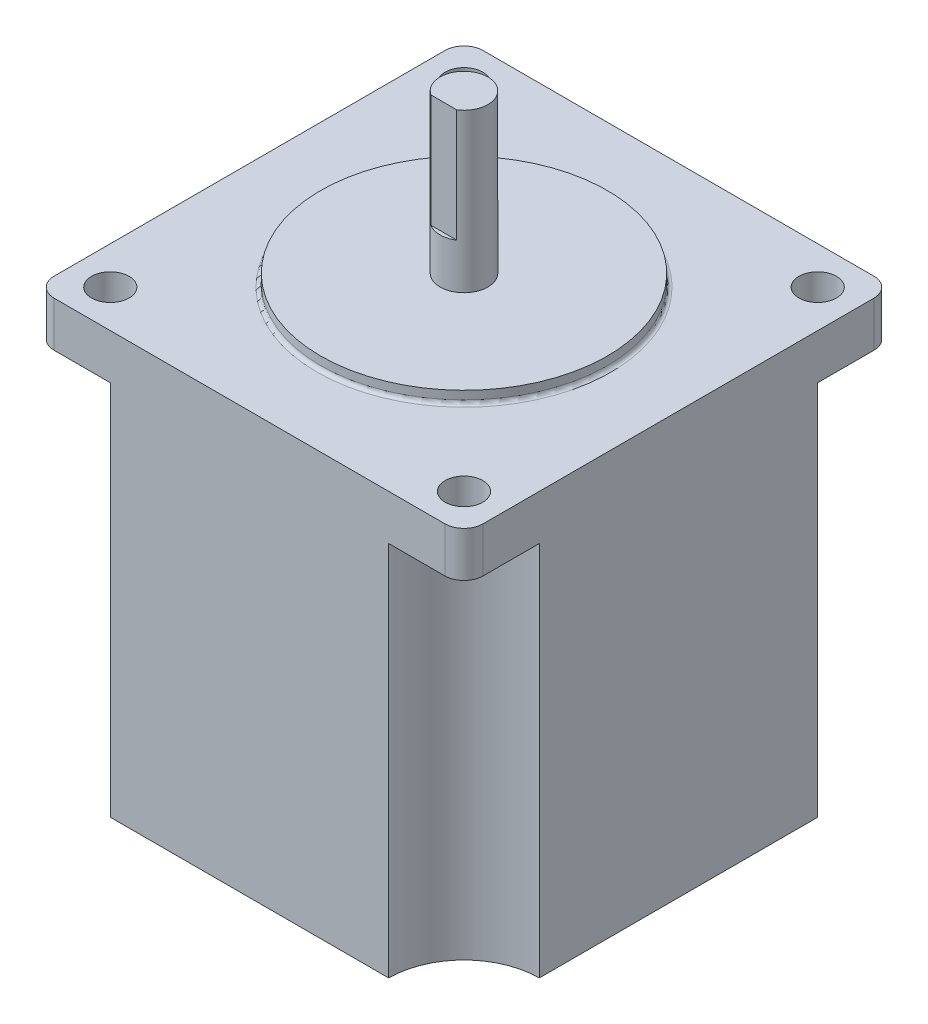
SolidWorks part; units mm, degrees
ref_plane "Front Plane" through (0, 0, 0) normal (0, 0, 1) x (1, 0, 0)
ref_plane "Top Plane" through (0, 0, 0) normal (0, 1, 0) x (1, 0, 0)
ref_plane "Right Plane" through (0, 0, 0) normal (1, 0, 0) x (0, 0, -1)
sketch "Sketch1" plane through (0, 0, 0) normal (0, 1, 0) x (1, 0, 0)
  line L1 (28.5, -28.5) -> (-28.5, -28.5)
  line L2 (28.5, -28.5) -> (28.5, 28.5)
  line L3 (28.5, 28.5) -> (-28.5, 28.5)
  line L4 (-28.5, -28.5) -> (-28.5, 28.5)
  line L5 (28.5, -28.5) -> (-28.5, 28.5) construction
  line L6 (28.5, 28.5) -> (-28.5, -28.5) construction
  point P0 (0, 0)
  dimension "D1" = 57
  dimension "D2" = 57
extrude "Boss-Extrude2" add sketch "Sketch1" along normal blind 56
sketch "Sketch2" plane through (0, 0, 0) normal (0, -1, 0) x (1, 0, 0)
  line L0 (28.5, -28.5) -> (-28.5, -28.5) construction
  line L1 (28.5, 28.5) -> (28.5, -28.5) construction
  line L2 (28.5, -18.5) -> (28.5, -28.5)
  line L3 (28.5, -28.5) -> (18.5, -28.5)
  line L4 (-28.5, -28.5) -> (-28.5, -18.5)
  line L5 (-18.5, -28.5) -> (-28.5, -28.5)
  line L6 (-28.5, 28.5) -> (-18.5, 28.5)
  line L7 (-28.5, 18.5) -> (-28.5, 28.5)
  line L8 (28.5, 28.5) -> (28.5, 18.5)
  line L9 (18.5, 28.5) -> (28.5, 28.5)
  arc A0 (18.5, -28.5) -> (28.5, -18.5) centre (28.5, -28.5) cw
  arc A1 (-28.5, -18.5) -> (-18.5, -28.5) centre (-28.5, -28.5) cw
  arc A2 (-18.5, 28.5) -> (-28.5, 18.5) centre (-28.5, 28.5) cw
  arc A3 (28.5, 18.5) -> (18.5, 28.5) centre (28.5, 28.5) cw
  point P20 (0, 0)
  dimension "D1" = 10
  dimension "D2" = 4
extrude "Cut-Extrude1" cut sketch "Sketch2" against normal blind 50
fillet "Fillet1" radius 2.54 4 edges at (-28.5, 53, -28.5) (28.5, 53, -28.5) (28.5, 53, 28.5) (-28.5, 53, 28.5)
sketch "Sketch3" plane through (0, 56, 0) normal (0, 1, 0) x (1, 0, 0)
  line L0 (-28.5, 25.96) -> (-28.5, -25.96) construction
  line L1 (-25.96, -28.5) -> (25.96, -28.5) construction
  circle A0 centre (-23.5, -23.5) radius 2.5
  circle A1 centre (-23.5, 23.5) radius 2.5
  circle A2 centre (23.5, 23.5) radius 2.5
  circle A3 centre (23.5, -23.5) radius 2.5
  point P15 (0, 0)
  dimension "D3" = 5
  dimension "D1" = 5
  dimension "D2" = 5
  dimension "D4" = 4
extrude "Cut-Extrude2" cut sketch "Sketch3" against normal blind 25.4
sketch "Sketch4" plane through (0, 56, 0) normal (0, 1, 0) x (1, 0, 0)
  circle A0 centre (0, 0) radius 19.05
  dimension "D1" = 38.1
extrude "Boss-Extrude3" add sketch "Sketch4" along normal blind 1.6
fillet "Fillet2" radius 0.5 1 edges at (0, 56, 19.05)
sketch "Sketch5" plane through (0, 57.6, 0) normal (0, 1, 0) x (1, 0, 0)
  circle A0 centre (0, 0) radius 3.175
  dimension "D1" = 6.35
extrude "Boss-Extrude4" add sketch "Sketch5" along normal blind 21
sketch "Sketch6" plane through (0, 78.6, 0) normal (0, 1, 0) x (1, 0, 0)
  line L0 (1.7103, -2.675) -> (-1.7103, -2.675)
  line L1 (0, -2.675) -> (0, 3.175) construction
  arc A2 (-1.7103, -2.675) -> (1.7103, -2.675) centre (0, 0) ccw
  dimension "D1" = 6.35
  dimension "D2" = 5.85
extrude "Cut-Extrude4" cut sketch "Sketch6" against normal blind 15
